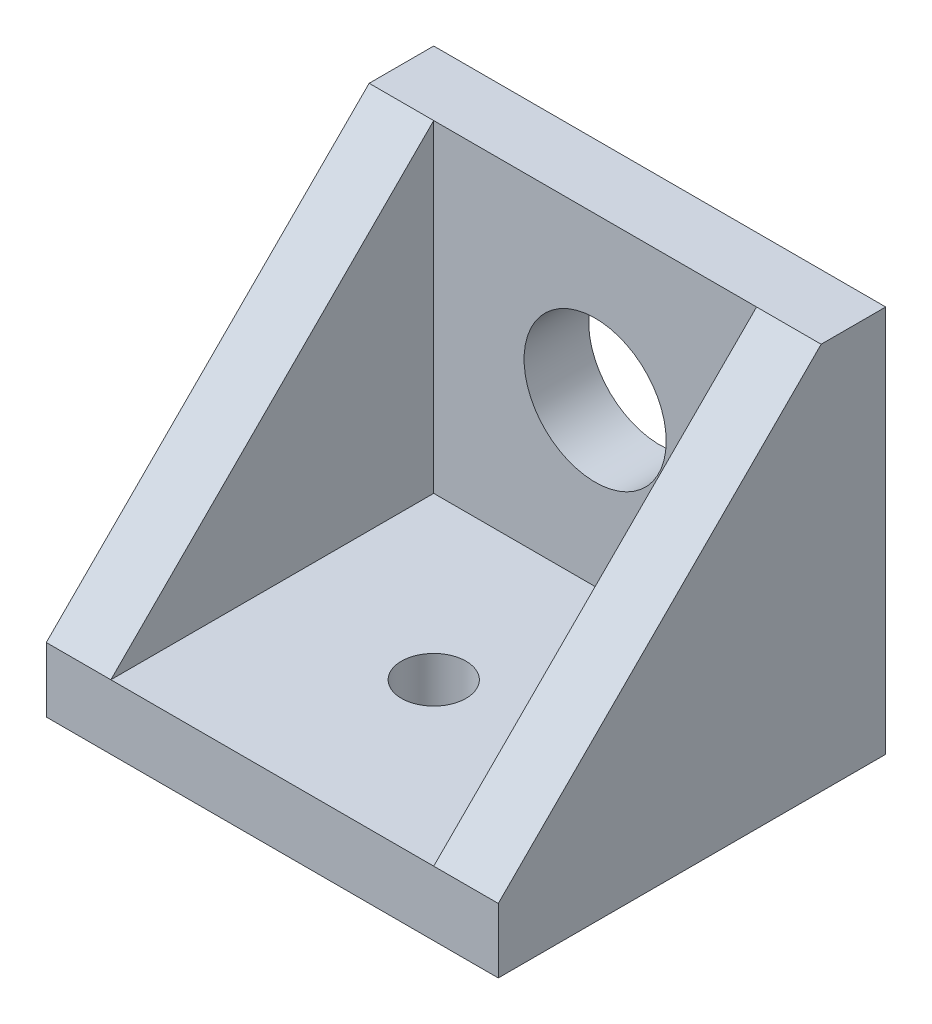
SolidWorks part; units mm, degrees
ref_plane "Front Plane" through (0, 0, 0) normal (0, 0, 1) x (1, 0, 0)
ref_plane "Top Plane" through (0, 0, 0) normal (0, 1, 0) x (1, 0, 0)
ref_plane "Right Plane" through (0, 0, 0) normal (1, 0, 0) x (0, 0, -1)
sketch "Sketch1" plane through (0, 0, 0) normal (0, 0, 1) x (1, 0, 0)
  line L1 (-7.5, -7.5) -> (7.5, -7.5)
  line L2 (-7.5, -7.5) -> (-7.5, 7.5)
  line L3 (-7.5, 7.5) -> (7.5, 7.5)
  line L4 (7.5, -7.5) -> (7.5, 7.5)
  line L5 (-7.5, -7.5) -> (7.5, 7.5) construction
  line L6 (-7.5, 7.5) -> (7.5, -7.5) construction
  circle A0 centre (0, 0) radius 3.302
  dimension "D1" = 6.604
  dimension "D2" = 15
extrude "Boss-Extrude1" add sketch "Sketch1" along normal blind 3
sketch "Sketch2" plane through (0, -7.5, 0) normal (0, -1, 0) x (1, 0, 0)
  line L5 (-7.5, 0) -> (7.5, 0)
  line L6 (-7.5, 0) -> (-7.5, 18)
  line L7 (-7.5, 18) -> (7.5, 18)
  line L8 (7.5, 0) -> (7.5, 18)
  circle A0 centre (0, 10.5) radius 1.5
  dimension "D3" = 3
  dimension "D1" = 18
  dimension "D2" = 15
  dimension "D4" = 10.5
extrude "Boss-Extrude2" add sketch "Sketch2" along normal blind 3
sketch "Sketch3" plane through (7.5, 0, 0) normal (1, 0, 0) x (0, 0, -1)
  line L1 (-18, -10.5) -> (-18, -7.5) construction
  line L2 (-18, -10.5) -> (-18, -7.5)
  line L3 (-3, 7.5) -> (0, 7.5) construction
  line L4 (0, -10.5) -> (0, 7.5) construction
  line L5 (0, -10.5) -> (-18, -10.5) construction
  line L6 (-3, 7.5) -> (0, 7.5)
  line L7 (0, -10.5) -> (0, 7.5)
  line L8 (0, -10.5) -> (-18, -10.5)
  line L9 (-18, -7.5) -> (-3, 7.5)
ref_plane "Plane1" through (0, 0, 0) normal (1, 0, 0) x (0, 0, -1)
extrude "Boss-Extrude3" add sketch "Sketch3" along normal blind 3
mirror "Mirror1" about plane through (0, 0, 0) normal (1, 0, 0) of "Boss-Extrude3"
